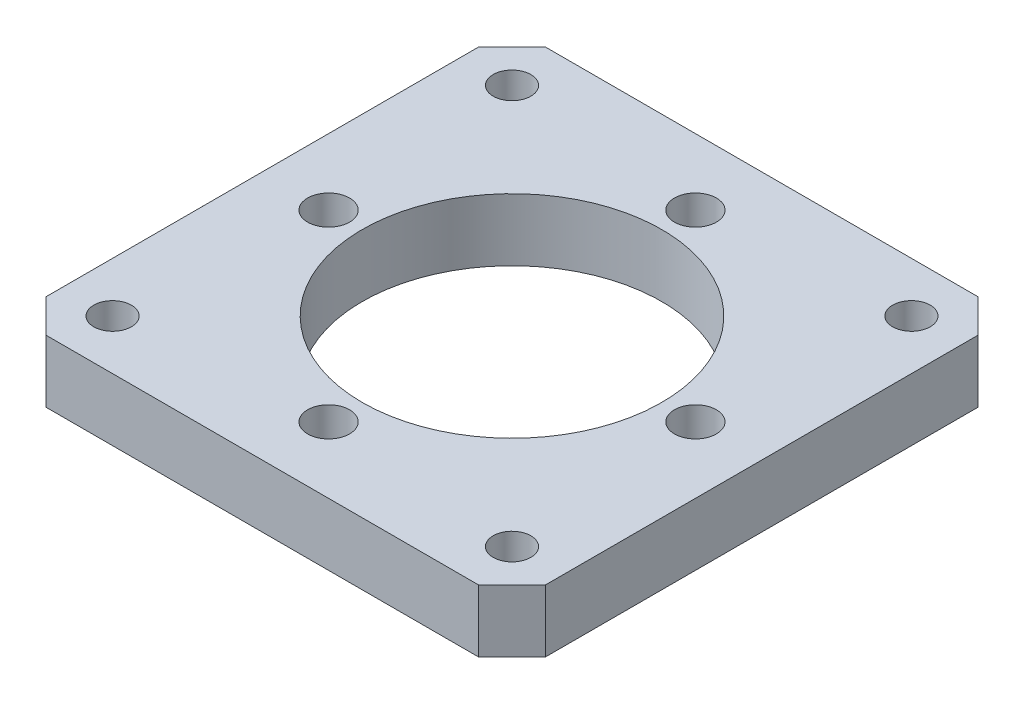
SolidWorks part; units mm, degrees
material "Alum Plate"
ref_plane "Front Plane" through (0, 0, 0) normal (0, 0, 1) x (1, 0, 0)
ref_plane "Top Plane" through (0, 0, 0) normal (0, 1, 0) x (1, 0, 0)
ref_plane "Right Plane" through (0, 0, 0) normal (1, 0, 0) x (0, 0, -1)
other "Bounding Box"
ref_plane "Default Plane" through (0, 2.286, 19.05) normal (0, -1, 0) x (-1, 0, 0)
sketch "Sketch1" plane through (0, 0, 0) normal (0, 1, 0) x (1, 0, 0)
  line L1 (-19.05, 19.05) -> (19.05, 19.05)
  line L2 (-19.05, 19.05) -> (-19.05, -19.05)
  line L3 (-19.05, -19.05) -> (19.05, -19.05)
  line L4 (19.05, 19.05) -> (19.05, -19.05)
  line L5 (-19.05, 19.05) -> (19.05, -19.05) construction
  line L6 (-19.05, -19.05) -> (19.05, 19.05) construction
  circle A0 centre (0, 0) radius 11.43
  point P0 (0, 0)
  dimension "D2" = 22.86
  dimension "D1" = 38.1
extrude "Boss-Extrude1" add sketch "Sketch1" along normal blind 4.7625
sketch "Sketch2" plane through (0, 4.7625, 0) normal (0, 1, 0) x (1, 0, 0)
  line L0 (0, 0) -> (0, 13.9954) construction
  line L1 (0, 0) -> (15.24, 15.24) construction
  line L2 (15.24, 15.24) -> (19.05, 15.24) construction
  line L3 (19.05, -19.05) -> (19.05, 19.05) construction
  line L4 (15.24, 15.24) -> (15.24, 19.05) construction
  line L5 (19.05, 19.05) -> (-19.05, 19.05) construction
  circle A0 centre (0, 13.9954) radius 1.6002
  circle A1 centre (15.24, 15.24) radius 1.4351
  dimension "D1" = 3.2004
  dimension "D3" = 2.8702
  dimension "D2" = 13.9954
  dimension "D4" = 3.81
extrude "Cut-Extrude1" cut sketch "Sketch2" against normal through all
pattern_circular "CirPattern1" count 4 over 360 about axis through (0, 0, 0) along (0, 1, 0) of "Cut-Extrude1"
chamfer "Chamfer1" distance 2.54 angle 45 4 edges at (-19.05, 2.3813, 19.05) (19.05, 2.3813, 19.05) (19.05, 2.3813, -19.05) (-19.05, 2.3813, -19.05)
equation "\"Unit Measure\"= \"BoundingVolume\" / \"Thickness\"'in^2"
